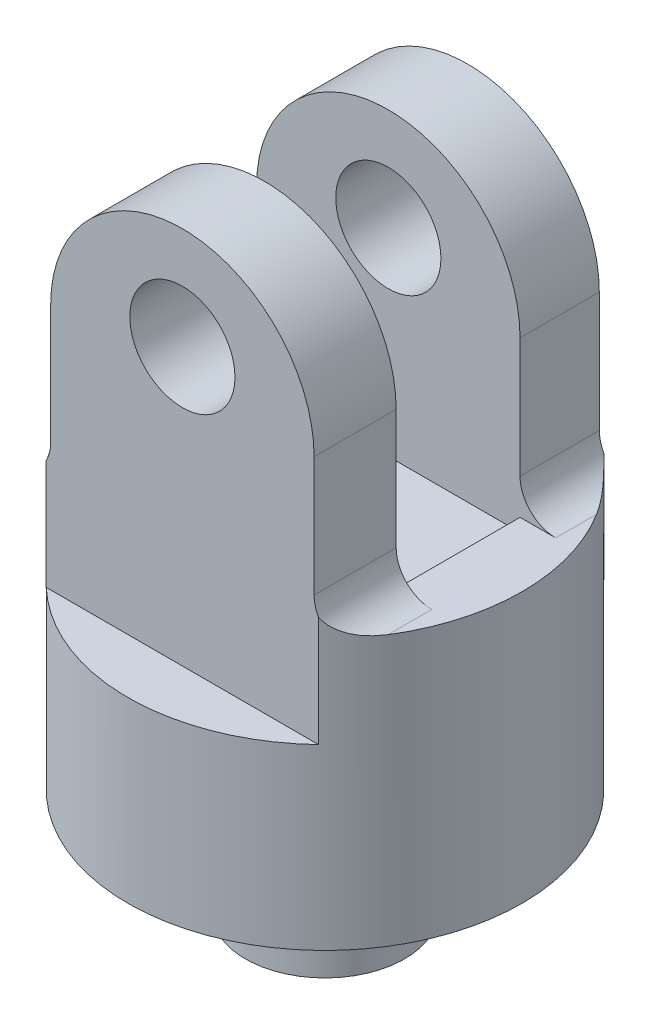
SolidWorks part; units mm, degrees
ref_plane "Front Plane" through (0, 0, 0) normal (0, 0, 1) x (1, 0, 0)
ref_plane "Top Plane" through (0, 0, 0) normal (0, 1, 0) x (1, 0, 0)
ref_plane "Right Plane" through (0, 0, 0) normal (1, 0, 0) x (0, 0, -1)
sketch "Sketch1" plane through (0, 0, 0) normal (0, 0, 1) x (1, 0, 0)
  line L0 (-53.6919, 3.6712) -> (-35.3357, 3.6712)
  line L1 (56.9043, 3.6712) -> (38.5481, 3.6712)
  line L2 (-35.3357, 3.6712) -> (-35.3357, 47.2673)
  line L3 (38.5481, 3.6712) -> (38.5481, 47.2673)
  line L4 (-53.6919, 3.6712) -> (-53.6919, -22.0275)
  line L5 (56.9043, 3.6712) -> (56.9043, -22.0275)
  line L6 (56.9043, -22.0275) -> (-53.6919, -22.0275)
  arc A0 (-35.3357, 47.2673) -> (38.5481, 47.2673) centre (1.6062, 47.2673) cw
extrude "Boss-Extrude1" add sketch "Sketch1" against normal blind 80
sketch "Sketch2" plane through (0, 0, 0) normal (0, 0, 1) x (1, 0, 0)
  circle A0 centre (1.6062, 55.4784) radius 14.753
extrude "Cut-Extrude1" cut sketch "Sketch2" against normal blind 80
sketch "Sketch3" plane through (0, -22.0275, 0) normal (0, -1, 0) x (1, 0, 0)
  line L0 (1.6062, 0) -> (1.6062, -80) construction
  line L1 (-53.6919, 0) -> (56.9043, 0) construction
  line L2 (-53.6919, -80) -> (56.9043, -80) construction
  circle A0 centre (1.6062, -40) radius 55.2981
extrude "Boss-Extrude2" add sketch "Sketch3" along normal blind 50
sketch "Sketch4" plane through (0, -72.0275, 0) normal (0, -1, 0) x (1, 0, 0)
  circle A0 centre (1.6062, -40) radius 22.3259
extrude "Boss-Extrude3" add sketch "Sketch4" along normal blind 30
sketch "Sketch5" plane through (0, -22.0275, 0) normal (0, -1, 0) x (1, 0, 0)
  line L0 (-36.576, 0) -> (-53.6919, 0)
  line L1 (-53.6919, 0) -> (-53.6919, -40)
  arc A0 (-53.6919, -40) -> (-36.576, 0) centre (1.6062, -40) cw
extrude "Cut-Extrude2" cut sketch "Sketch5" against normal blind 30
sketch "Sketch6" plane through (0, -22.0275, 0) normal (0, -1, 0) x (1, 0, 0)
  line L0 (-36.576, -80) -> (-53.6919, -80)
  line L1 (-53.6919, -80) -> (-53.6919, -40)
  arc A0 (-53.6919, -40) -> (-36.576, -80) centre (1.6062, -40) ccw
extrude "Cut-Extrude3" cut sketch "Sketch6" against normal blind 30
sketch "Sketch7" plane through (0, -22.0275, 0) normal (0, -1, 0) x (1, 0, 0)
  line L0 (56.9043, -40) -> (56.9043, 0)
  line L1 (56.9043, 0) -> (39.7884, 0)
  arc A0 (39.7884, 0) -> (56.9043, -40) centre (1.6062, -40) cw
extrude "Cut-Extrude4" cut sketch "Sketch7" against normal blind 30
sketch "Sketch8" plane through (0, -22.0275, 0) normal (0, -1, 0) x (1, 0, 0)
  line L0 (39.7884, -80) -> (56.9043, -80)
  line L1 (56.9043, -80) -> (56.9043, -40)
  arc A0 (56.9043, -40) -> (39.7884, -80) centre (1.6062, -40) cw
extrude "Cut-Extrude5" cut sketch "Sketch8" against normal blind 30
sketch "Sketch11" plane through (0, 0, 0) normal (0, 1, 0) x (1, 0, 0)
  line L0 (-35.3357, 80) -> (-35.3357, 0) construction
  line L5 (-35.3357, 57.7614) -> (38.5481, 57.7614)
  line L6 (-35.3357, 57.7614) -> (-35.3357, 23.0222)
  line L7 (-35.3357, 23.0222) -> (38.5481, 23.0222)
  line L8 (38.5481, 57.7614) -> (38.5481, 23.0222)
  line L9 (38.5481, 80) -> (38.5481, 0) construction
extrude "Cut-Extrude9" cut sketch "Sketch11" along normal blind 110
fillet "Fillet1" radius 10 4 edges at (-35.3357, 3.6712, -68.8807) (38.5481, 3.6712, -68.8807) (38.5481, 3.6712, -11.5111) (-35.3357, 3.6712, -11.5111)
sketch "Sketch12" plane through (0, -102.0275, 0) normal (0, -1, 0) x (1, 0, 0)
  circle A0 centre (1.6062, -40) radius 9.5077
extrude "Cut-Extrude10" cut sketch "Sketch12" against normal blind 110
